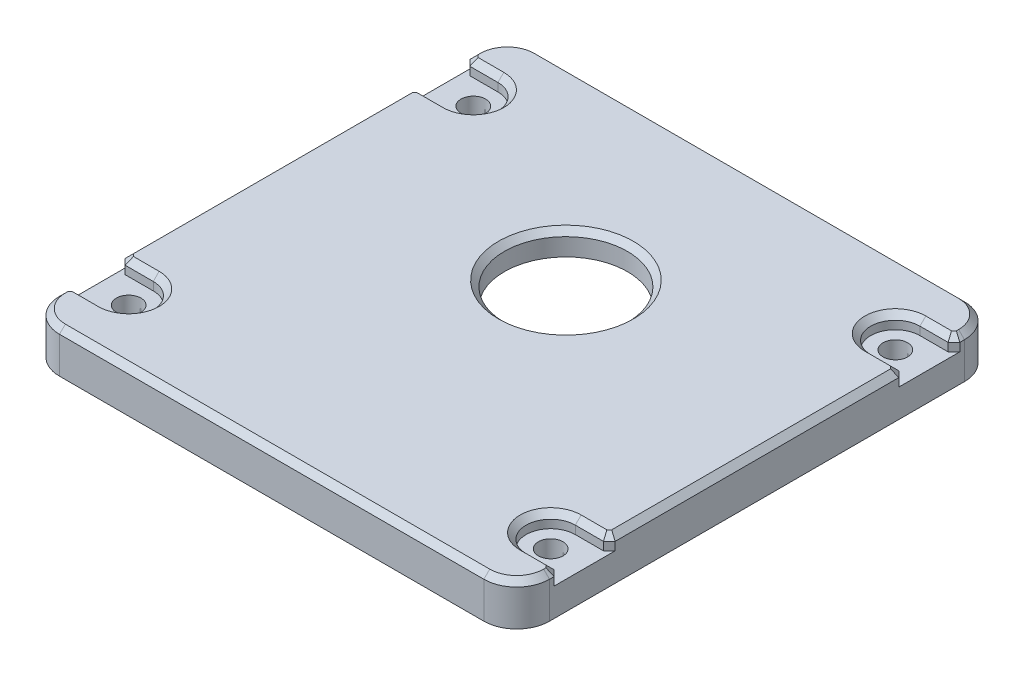
SolidWorks part; units mm, degrees
ref_plane "Front Plane" through (0, 0, 0) normal (0, 0, 1) x (1, 0, 0)
ref_plane "Top Plane" through (0, 0, 0) normal (0, 1, 0) x (1, 0, 0)
ref_plane "Right Plane" through (0, 0, 0) normal (1, 0, 0) x (0, 0, -1)
sketch "Sketch1" plane through (0, 0, 0) normal (0, 1, 0) x (1, 0, 0)
  line L1 (-18.1, 18.7) -> (18.1, 18.7)
  line L2 (-18.1, 18.7) -> (-18.1, -18.7)
  line L3 (-18.1, -18.7) -> (18.1, -18.7)
  line L4 (18.1, 18.7) -> (18.1, -18.7)
  line L5 (-18.1, 18.7) -> (18.1, -18.7) construction
  line L6 (-18.1, -18.7) -> (18.1, 18.7) construction
  line L11 (-20.9, 20.5) -> (20.9, 20.5)
  line L12 (-20.9, 20.5) -> (-20.9, -20.5)
  line L13 (-20.9, -20.5) -> (20.9, -20.5)
  line L14 (20.9, 20.5) -> (20.9, -20.5)
  line L15 (-20.9, 20.5) -> (20.9, -20.5) construction
  line L16 (-20.9, -20.5) -> (20.9, 20.5) construction
  point P0 (0, 0)
  point P6 (0, 0)
  dimension "D4" = 2.8
  dimension "D1" = 37.4
  dimension "D2" = 36.2
  dimension "D3" = 1.8
extrude "Boss-Extrude1" add sketch "Sketch1" along normal blind 3
fillet "Fillet1" radius 2.8 4 edges at (20.9, 1.5, 20.5) (20.9, 1.5, -20.5) (-20.9, 1.5, -20.5) (-20.9, 1.5, 20.5)
sketch "Sketch2" plane through (0, 0, 0) normal (0, -1, 0) x (1, 0, 0)
  line L0 (20.1, -17.7) -> (20.1, 17.7)
  line L1 (18.1, 19.7) -> (-18.1, 19.7)
  line L2 (-20.1, 17.7) -> (-20.1, -17.7)
  line L3 (-18.1, -19.7) -> (18.1, -19.7)
  line L4 (20.9, -17.7) -> (20.9, 17.7)
  line L5 (18.1, 20.5) -> (-18.1, 20.5)
  line L6 (-20.9, 17.7) -> (-20.9, -17.7)
  line L7 (-18.1, -20.5) -> (18.1, -20.5)
  line L8 (20.9, -17.7) -> (20.9, 17.7)
  line L9 (18.1, 20.5) -> (-18.1, 20.5)
  line L10 (-20.9, 17.7) -> (-20.9, -17.7)
  line L11 (-18.1, -20.5) -> (18.1, -20.5)
  arc A0 (20.1, 17.7) -> (18.1, 19.7) centre (18.1, 17.7) ccw
  arc A1 (-18.1, 19.7) -> (-20.1, 17.7) centre (-18.1, 17.7) ccw
  arc A2 (-20.1, -17.7) -> (-18.1, -19.7) centre (-18.1, -17.7) ccw
  arc A3 (18.1, -19.7) -> (20.1, -17.7) centre (18.1, -17.7) ccw
  arc A4 (20.9, 17.7) -> (18.1, 20.5) centre (18.1, 17.7) ccw
  arc A5 (-18.1, 20.5) -> (-20.9, 17.7) centre (-18.1, 17.7) ccw
  arc A6 (-20.9, -17.7) -> (-18.1, -20.5) centre (-18.1, -17.7) ccw
  arc A7 (18.1, -20.5) -> (20.9, -17.7) centre (18.1, -17.7) ccw
  arc A8 (20.9, 17.7) -> (18.1, 20.5) centre (18.1, 17.7) ccw
  arc A9 (-18.1, 20.5) -> (-20.9, 17.7) centre (-18.1, 17.7) ccw
  arc A10 (-20.9, -17.7) -> (-18.1, -20.5) centre (-18.1, -17.7) ccw
  arc A11 (18.1, -20.5) -> (20.9, -17.7) centre (18.1, -17.7) ccw
  dimension "D1" = 0
  dimension "D2" = 0.8
extrude "Boss-Extrude2" add sketch "Sketch2" along normal blind 0.6
sketch "Sketch4" plane through (0, 3, 0) normal (0, 1, 0) x (1, 0, 0)
  line L0 (0, 0) -> (0, 20.5) construction
  line L1 (18.1, 20.5) -> (-18.1, 20.5) construction
  line L2 (0, 0) -> (-20.9, 0) construction
  line L3 (-20.9, 17.7) -> (-20.9, -17.7) construction
  line L4 (-18, 15.75) -> (-18.1, 15.75)
  line L5 (-18.1, 18.7) -> (-18.1, -18.7) construction
  line L6 (-18, 13.65) -> (-18.1, 13.65)
  line L7 (-15.55, 18.7) -> (-15.55, 14.7)
  line L8 (18.1, 18.7) -> (-18.1, 18.7) construction
  line L9 (-18, 12.25) -> (-18.1, 12.25)
  line L10 (-18.1, 12.25) -> (-18.1, 13.65)
  line L11 (-18.1, 15.75) -> (-18.1, 18.7)
  line L12 (-18.1, 18.7) -> (-15.55, 18.7)
  line L13 (18.1, 15.75) -> (18.1, 18.7)
  line L14 (18, 15.75) -> (18.1, 15.75)
  line L15 (18, 13.65) -> (18.1, 13.65)
  line L16 (18.1, 12.25) -> (18.1, 13.65)
  line L17 (18, 12.25) -> (18.1, 12.25)
  line L18 (15.55, 18.7) -> (15.55, 14.7)
  line L19 (18.1, 18.7) -> (15.55, 18.7)
  line L20 (18, -15.75) -> (18.1, -15.75)
  line L21 (18, -13.65) -> (18.1, -13.65)
  line L22 (18.1, -12.25) -> (18.1, -13.65)
  line L23 (18, -12.25) -> (18.1, -12.25)
  line L24 (15.55, -18.7) -> (15.55, -14.7)
  line L25 (18.1, -18.7) -> (15.55, -18.7)
  line L26 (18.1, -15.75) -> (18.1, -18.7)
  line L27 (-18.1, -15.75) -> (-18.1, -18.7)
  line L28 (-18, -15.75) -> (-18.1, -15.75)
  line L29 (-18, -13.65) -> (-18.1, -13.65)
  line L30 (-18.1, -12.25) -> (-18.1, -13.65)
  line L31 (-18, -12.25) -> (-18.1, -12.25)
  line L32 (-15.55, -18.7) -> (-15.55, -14.7)
  line L33 (-18.1, -18.7) -> (-15.55, -18.7)
  arc A0 (-18, 15.75) -> (-18, 13.65) centre (-18, 14.7) cw
  arc A1 (-15.55, 14.7) -> (-18, 12.25) centre (-18, 14.7) cw
  arc A2 (18, 15.75) -> (18, 13.65) centre (18, 14.7) ccw
  arc A3 (15.55, 14.7) -> (18, 12.25) centre (18, 14.7) ccw
  arc A4 (18, -15.75) -> (18, -13.65) centre (18, -14.7) cw
  arc A5 (15.55, -14.7) -> (18, -12.25) centre (18, -14.7) cw
  arc A6 (-18, -15.75) -> (-18, -13.65) centre (-18, -14.7) ccw
  arc A7 (-15.55, -14.7) -> (-18, -12.25) centre (-18, -14.7) ccw
  dimension "D3" = 1.05
  dimension "D4" = 1.4
  dimension "D1" = 36
  dimension "D2" = 29.4
extrude "Boss-Extrude3" add sketch "Sketch4" against normal blind 4.4
sketch "Sketch5" plane through (0, 3, 0) normal (0, 1, 0) x (1, 0, 0)
  line L0 (0, 0) -> (0, 20.5) construction
  line L1 (18.1, 20.5) -> (-18.1, 20.5) construction
  line L2 (0, 0) -> (-20.9, 0) construction
  line L3 (-20.9, 17.7) -> (-20.9, -17.7) construction
  circle A0 centre (-18, 14.7) radius 1.05
  circle A1 centre (18, 14.7) radius 1.05
  circle A2 centre (18, -14.7) radius 1.05
  circle A3 centre (-18, -14.7) radius 1.05
extrude "Cut-Extrude1" cut sketch "Sketch5" against normal through all
sketch "Sketch6" plane through (0, 3, 0) normal (0, 1, 0) x (1, 0, 0)
  line L0 (15.55, -14.7) -> (15.55, -18.7) construction
  line L1 (-15.55, -18.7) -> (15.55, -18.7)
  line L2 (-15.55, -18.7) -> (-15.55, -16.9)
  line L3 (-15.55, -16.9) -> (15.55, -16.9)
  line L4 (15.55, -18.7) -> (15.55, -16.9)
  line L5 (15.55, 18.7) -> (15.55, 14.7) construction
  line L6 (-15.55, 18.7) -> (15.55, 18.7)
  line L7 (-15.55, 18.7) -> (-15.55, 16.9)
  line L8 (-15.55, 16.9) -> (15.55, 16.9)
  line L9 (15.55, 18.7) -> (15.55, 16.9)
  line L12 (-18.1, 12.25) -> (-18, 12.25) construction
  line L14 (0, 0) -> (0, 20.5) construction
  line L15 (18.1, 20.5) -> (-18.1, 20.5) construction
  line L16 (-18.1, 12.25) -> (-18, 12.25)
  line L17 (0, 0) -> (-20.9, 0) construction
  line L18 (-15.55, 14.7) -> (-15.55, 11.25)
  line L19 (-15.55, 11.25) -> (-18.1, 11.25)
  line L20 (-18.1, 12.25) -> (-18.1, -12.25) construction
  line L21 (-18.1, 11.25) -> (-18.1, 12.25)
  line L22 (-20.9, 17.7) -> (-20.9, -17.7) construction
  line L23 (-15.55, -11.25) -> (-18.1, -11.25)
  line L24 (-15.55, -14.7) -> (-15.55, -11.25)
  line L25 (-18.1, -12.25) -> (-18, -12.25)
  line L26 (-18.1, -11.25) -> (-18.1, -12.25)
  line L27 (15.55, -14.7) -> (15.55, -11.25)
  line L28 (18.1, -12.25) -> (18, -12.25)
  line L29 (18.1, -11.25) -> (18.1, -12.25)
  line L30 (15.55, -11.25) -> (18.1, -11.25)
  line L31 (15.55, 11.25) -> (18.1, 11.25)
  line L32 (15.55, 14.7) -> (15.55, 11.25)
  line L33 (18.1, 12.25) -> (18, 12.25)
  line L34 (18.1, 11.25) -> (18.1, 12.25)
  arc A2 (-18, 12.25) -> (-15.55, 14.7) centre (-18, 14.7) ccw construction
  arc A6 (-18, 12.25) -> (-15.55, 14.7) centre (-18, 14.7) ccw
  arc A8 (-18, -12.25) -> (-15.55, -14.7) centre (-18, -14.7) cw
  arc A9 (18, -12.25) -> (15.55, -14.7) centre (18, -14.7) ccw
  arc A10 (18, 12.25) -> (15.55, 14.7) centre (18, 14.7) cw
  dimension "D1" = 1.8
  dimension "D2" = 1.8
  dimension "D3" = 1
extrude "Boss-Extrude4" add sketch "Sketch6" against normal up to surface (4.4 mm away) up to face at (-17.327, -1.4, -14.9881)
fillet "Fillet2" radius 1 8 edges at (-15.55, 0.8, 16.9) (15.55, 0.8, 16.9) (-15.55, 0.8, -16.9) (15.55, 0.8, -16.9) (-15.55, 0.8, 11.25) (15.55, 0.8, 11.25) (-15.55, 0.8, -11.25) (15.55, 0.8, -11.25)
sketch "Sketch7" plane through (0, -1.4, 0) normal (0, -1, 0) x (1, 0, 0)
  line L0 (-18, 18.6) -> (-18, -18.6)
  line L1 (-18.1, 18.7) -> (18.1, 18.7)
  line L2 (-18.1, 18.7) -> (-18.1, -18.7)
  line L3 (-18.1, -18.7) -> (18.1, -18.7)
  line L4 (18.1, 18.7) -> (18.1, -18.7)
  line L5 (-18, -18.6) -> (18, -18.6)
  line L6 (18, 18.6) -> (18, -18.6)
  line L7 (-18, 18.6) -> (18, 18.6)
  dimension "D1" = 0.1
extrude "Cut-Extrude2" cut sketch "Sketch7" against normal up to surface (1.4 mm away) up to face at (0, 0, 0)
fillet "Fillet3" radius 0.5 16 edges at (-18, -0.7, -18.6) (-18, -0.7, -15.75) (-18, -0.7, -13.65) (-18, -0.7, -11.25) (18, -0.7, -18.6) (18, -0.7, -15.75) (18, -0.7, -13.65) (18, -0.7, -11.25) (18, -0.7, 13.65) (18, -0.7, 11.25) (18, -0.7, 15.75) (18, -0.7, 18.6) (-18, -0.7, 18.6) (-18, -0.7, 15.75) (-18, -0.7, 13.65) (-18, -0.7, 11.25)
fillet "Fillet4" radius 0.6 4 edges at (18.1, 1.5, -11.25) (-18.1, 1.5, -11.25) (-18.1, 1.5, 11.25) (18.1, 1.5, 11.25)
sketch "Sketch8" plane through (0, 3, 0) normal (0, 1, 0) x (1, 0, 0)
  line L0 (0, 0) -> (-20.9, 0) construction
  line L1 (0, 0) -> (0, 20.5) construction
  line L4 (-18.1, -20.5) -> (18.1, -20.5)
  line L5 (20.9, -17.7) -> (20.9, 17.7)
  line L6 (18.1, 20.5) -> (-18.1, 20.5)
  line L7 (-20.9, 17.7) -> (-20.9, -17.7)
  line L8 (-18.1, -20.5) -> (18.1, -20.5)
  line L9 (20.9, -17.7) -> (20.9, 17.7)
  line L10 (18.1, 20.5) -> (-18.1, 20.5)
  line L11 (-20.9, 17.7) -> (-20.9, -17.7)
  circle A0 centre (-18, 14.7) radius 1.05
  circle A1 centre (18, 14.7) radius 1.05
  circle A2 centre (18, -14.7) radius 1.05
  circle A3 centre (-18, -14.7) radius 1.05
  arc A4 (18.1, -20.5) -> (20.9, -17.7) centre (18.1, -17.7) ccw
  arc A5 (20.9, 17.7) -> (18.1, 20.5) centre (18.1, 17.7) ccw
  arc A6 (-18.1, 20.5) -> (-20.9, 17.7) centre (-18.1, 17.7) ccw
  arc A7 (-20.9, -17.7) -> (-18.1, -20.5) centre (-18.1, -17.7) ccw
  arc A8 (18.1, -20.5) -> (20.9, -17.7) centre (18.1, -17.7) ccw
  arc A9 (20.9, 17.7) -> (18.1, 20.5) centre (18.1, 17.7) ccw
  arc A10 (-18.1, 20.5) -> (-20.9, 17.7) centre (-18.1, 17.7) ccw
  arc A11 (-20.9, -17.7) -> (-18.1, -20.5) centre (-18.1, -17.7) ccw
  circle A12 centre (0, 4.6) radius 5.25
  dimension "D3" = 10.5
  dimension "D2" = 25.1
  dimension "D1" = 0
extrude "Boss-Extrude5" add sketch "Sketch8" against normal blind 2
sketch "Sketch9" plane through (0, 3, 0) normal (0, 1, 0) x (1, 0, 0)
  line L0 (-18, 14.7) -> (-20.9, 14.7) construction
  line L1 (-20.9, 17.7) -> (-20.9, -17.7) construction
  line L2 (-18, 12.6) -> (-20.9, 12.6)
  line L3 (-18, 16.8) -> (-20.9, 16.8)
  line L4 (0, 0) -> (0, 20.5) construction
  line L5 (18.1, 20.5) -> (-18.1, 20.5) construction
  line L6 (0, 0) -> (-20.9, 0) construction
  line L7 (18, 14.7) -> (20.9, 14.7) construction
  line L8 (18, 12.6) -> (20.9, 12.6)
  line L9 (18, 16.8) -> (20.9, 16.8)
  line L10 (18, -14.7) -> (20.9, -14.7) construction
  line L11 (18, -12.6) -> (20.9, -12.6)
  line L12 (18, -16.8) -> (20.9, -16.8)
  line L13 (-18, -14.7) -> (-20.9, -14.7) construction
  line L14 (-18, -12.6) -> (-20.9, -12.6)
  line L15 (-18, -16.8) -> (-20.9, -16.8)
  arc A0 (-18, 12.6) -> (-18, 16.8) centre (-18, 14.7) ccw
  arc A1 (-20.9, 16.8) -> (-20.9, 12.6) centre (-20.9, 14.7) ccw
  arc A2 (18, 12.6) -> (18, 16.8) centre (18, 14.7) cw
  arc A3 (20.9, 16.8) -> (20.9, 12.6) centre (20.9, 14.7) cw
  arc A4 (18, -12.6) -> (18, -16.8) centre (18, -14.7) ccw
  arc A5 (20.9, -16.8) -> (20.9, -12.6) centre (20.9, -14.7) ccw
  arc A6 (-18, -12.6) -> (-18, -16.8) centre (-18, -14.7) cw
  arc A7 (-20.9, -16.8) -> (-20.9, -12.6) centre (-20.9, -14.7) cw
  point P5 (-19.45, 14.7)
  point P18 (19.45, 14.7)
  point P25 (19.45, -14.7)
  point P32 (-19.45, -14.7)
  dimension "D1" = 4.2
extrude "Cut-Extrude3" cut sketch "Sketch9" against normal blind 1.2
chamfer "Chamfer1" distance 0.5 angle 45 8 edges at (-20.9, 2.4, 16.8) (-20.9, 2.4, 12.6) (20.9, 2.4, 16.8) (20.9, 2.4, 12.6) (20.9, 2.4, -12.6) (20.9, 2.4, -16.8) (-20.9, 2.4, -12.6) (-20.9, 2.4, -16.8)
chamfer "Chamfer2" distance 0.5 angle 45 33 edges at (0, 3, 0.65) (-15.9, 3, 14.7) (-19.2, 3, 12.6) (-20.65, 3, 12.35) (-20.9, 3, 0) (-20.65, 3, -12.35) (-19.2, 3, -12.6) (-15.9, 3, -14.7) (-19.2, 3, -16.8) (-20.65, 3, -17.05) (-20.9, 3, -17.5) (-20.0799, 3, -19.6799) (0, 3, -20.5) (20.0799, 3, -19.6799) (20.9, 3, -17.5) (20.65, 3, -17.05) (19.2, 3, -16.8) (15.9, 3, -14.7) (19.2, 3, -12.6) (20.65, 3, -12.35) (20.9, 3, 0) (20.65, 3, 12.35) (19.2, 3, 12.6) (15.9, 3, 14.7) (19.2, 3, 16.8) (20.65, 3, 17.05) (20.9, 3, 17.5) (20.0799, 3, 19.6799) (0, 3, 20.5) (-20.0799, 3, 19.6799) (-20.9, 3, 17.5) (-20.65, 3, 17.05) (-19.2, 3, 16.8)
